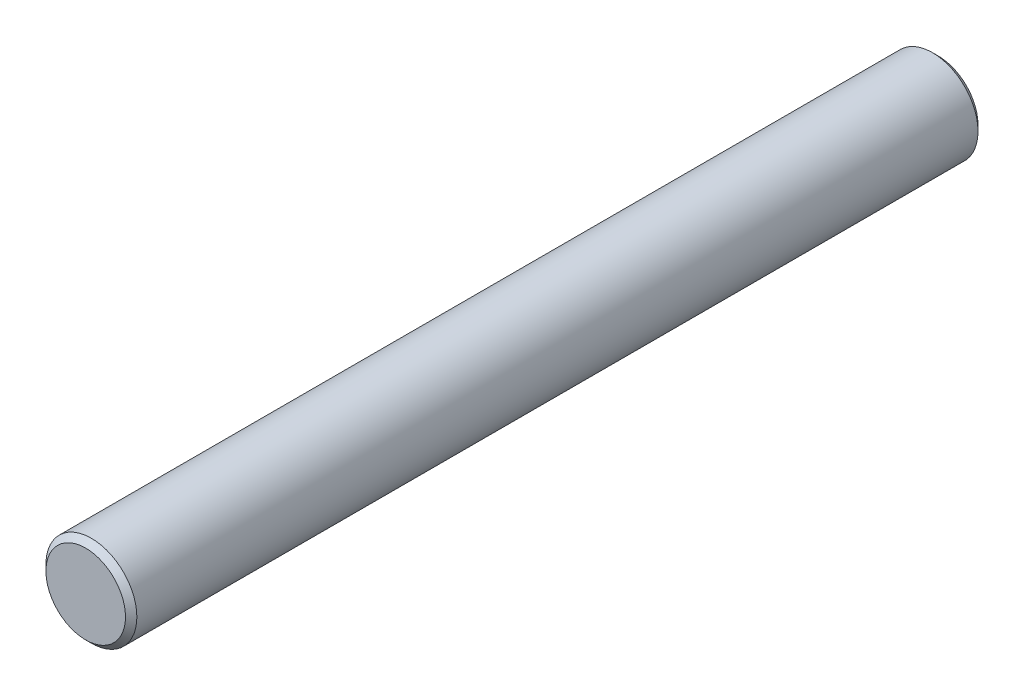
SolidWorks part; units mm, degrees
material "Plain Carbon Steel"
ref_plane "Front Plane" through (0, 0, 0) normal (0, 0, 1) x (1, 0, 0)
ref_plane "Top Plane" through (0, 0, 0) normal (0, 1, 0) x (1, 0, 0)
ref_plane "Right Plane" through (0, 0, 0) normal (1, 0, 0) x (0, 0, -1)
sketch "Sketch1" plane through (0, 0, 0) normal (0, 0, 1) x (1, 0, 0)
  circle A0 centre (0, 0) radius 4
  dimension "D1" = 8
extrude "Boss-Extrude1" add sketch "Sketch1" along normal blind 75
chamfer "Chamfer1" distance 0.5 angle 45 2 edges at (4, 0, 0) (4, 0, 75)
